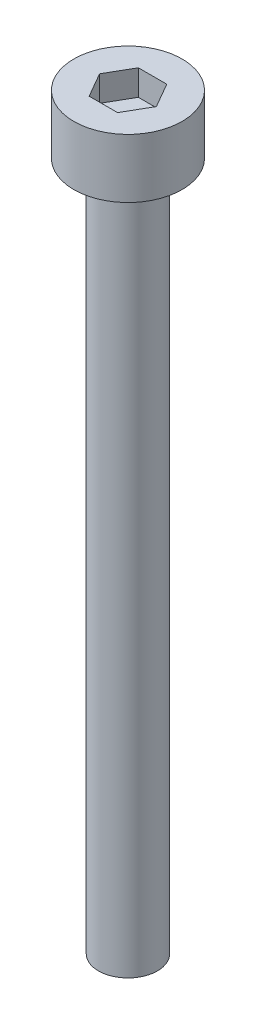
SolidWorks part; units mm, degrees
material "AISI 304"
ref_plane "前视基准面" through (0, 0, 0) normal (0, 0, 1) x (1, 0, 0)
ref_plane "上视基准面" through (0, 0, 0) normal (0, 1, 0) x (1, 0, 0)
ref_plane "右视基准面" through (0, 0, 0) normal (1, 0, 0) x (0, 0, -1)
sketch "草图1" plane through (0, 0, 0) normal (0, 1, 0) x (1, 0, 0)
  circle A0 centre (0, 0) radius 2.75
  dimension "D1" = 5.5
extrude "杯头" add sketch "草图1" along normal blind 3
sketch "草图2" plane through (0, 3, 0) normal (0, 1, 0) x (1, 0, 0)
  line L1 (1.4434, 0) -> (0.7217, 1.25)
  line L2 (0.7217, 1.25) -> (-0.7217, 1.25)
  line L3 (-0.7217, 1.25) -> (-1.4434, 0)
  line L4 (-1.4434, 0) -> (-0.7217, -1.25)
  line L5 (-0.7217, -1.25) -> (0.7217, -1.25)
  line L6 (0.7217, -1.25) -> (1.4434, 0)
  circle A0 centre (0, 0) radius 1.25 construction
  dimension "D1" = 2.5
extrude "内六角口" cut sketch "草图2" against normal blind 1.3
sketch "草图3" plane through (0, 0, 0) normal (0, -1, 0) x (1, 0, 0)
  circle A0 centre (0, 0) radius 1.5
  dimension "D1" = 3
extrude "螺纹长" add sketch "草图3" along normal blind 35
